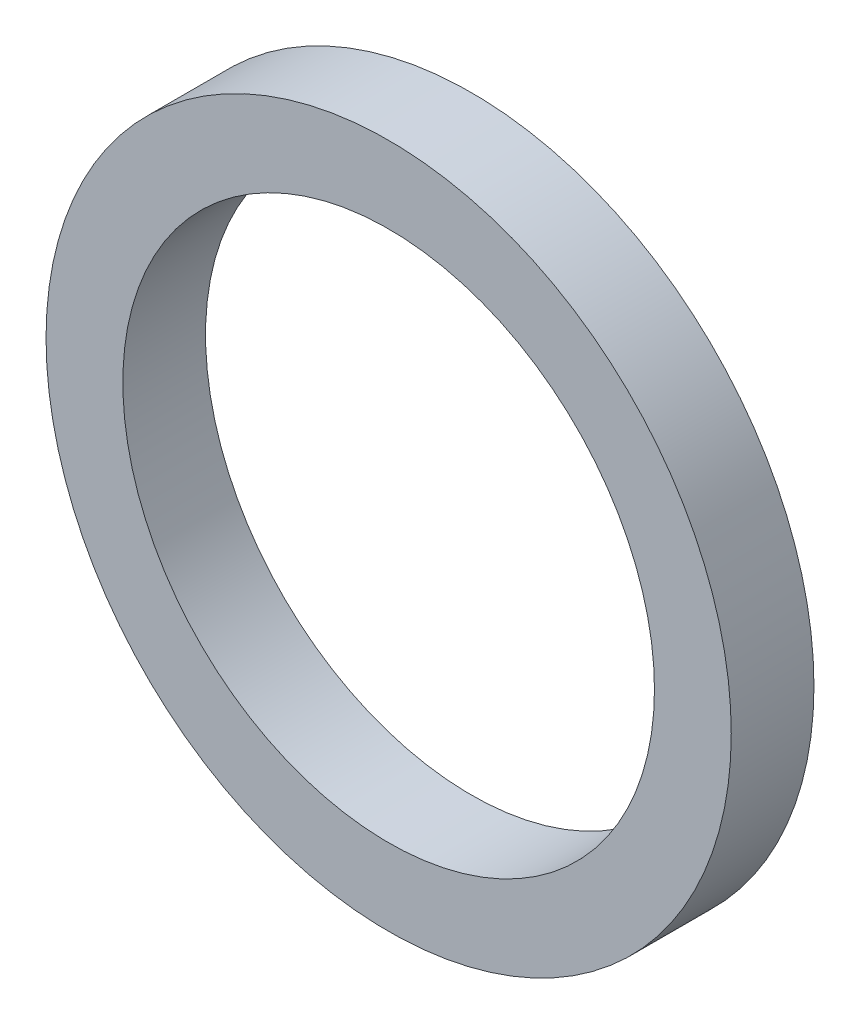
SolidWorks part; units mm, degrees
ref_plane "前视基准面" through (0, 0, 0) normal (0, 0, 1) x (1, 0, 0)
ref_plane "上视基准面" through (0, 0, 0) normal (0, 1, 0) x (1, 0, 0)
ref_plane "右视基准面" through (0, 0, 0) normal (1, 0, 0) x (0, 0, -1)
sketch "草图1" plane through (0, 0, 0) normal (0, 0, 1) x (1, 0, 0)
  circle A0 centre (0, 0) radius 22.5
  circle A1 centre (0, 0) radius 29
  dimension "D1" = 45
  dimension "D2" = 58
extrude "凸台-拉伸1" add sketch "草图1" along normal blind 7
shell "抽壳1" thickness 1
